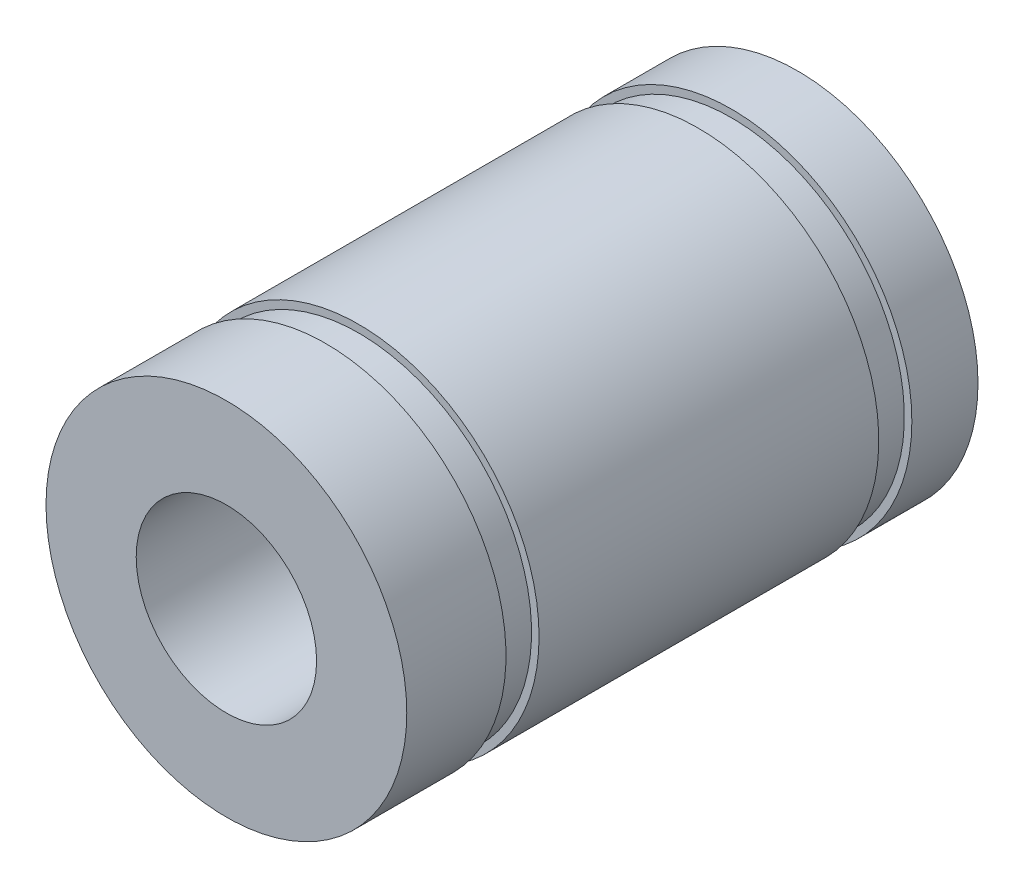
SolidWorks part; units mm, degrees
ref_plane "Front Plane" through (0, 0, 0) normal (0, 0, 1) x (1, 0, 0)
ref_plane "Top Plane" through (0, 0, 0) normal (0, 1, 0) x (1, 0, 0)
ref_plane "Right Plane" through (0, 0, 0) normal (1, 0, 0) x (0, 0, -1)
sketch "Sketch1" plane through (0, 0, 0) normal (0, 0, 1) x (1, 0, 0)
  circle A0 centre (0, 0) radius 3
  circle A1 centre (0, 0) radius 6
  dimension "D1" = 6
  dimension "D2" = 12
extrude "Boss-Extrude1" add sketch "Sketch1" along normal blind 19
sketch "Sketch2" plane through (0, 0, 0) normal (0, 1, 0) x (1, 0, 0)
  line L0 (0, 0) -> (0, -19) construction
  line L1 (-6, -19) -> (6, -19) construction
  line L2 (6, -19) -> (6, 0) construction
  line L3 (5.75, -2.2) -> (7.5998, -2.2)
  line L4 (5.75, -2.2) -> (5.75, -3.3)
  line L5 (5.75, -3.3) -> (7.5998, -3.3)
  line L6 (7.5998, -2.2) -> (7.5998, -3.3)
  line L7 (5.75, -15.7) -> (7.5998, -15.7)
  line L8 (5.75, -15.7) -> (5.75, -14.6)
  line L9 (5.75, -14.6) -> (7.5998, -14.6)
  line L10 (7.5998, -15.7) -> (7.5998, -14.6)
  line L11 (5.75, -3.3) -> (5.75, -15.7) construction
  line L12 (5.75, -9.5) -> (0, -9.5) construction
  dimension "D1" = 1.1
  dimension "D2" = 0.25
  dimension "D3" = 13.5
revolve "Cut-Revolve1" cut sketch "Sketch2" angle 360 about L0
